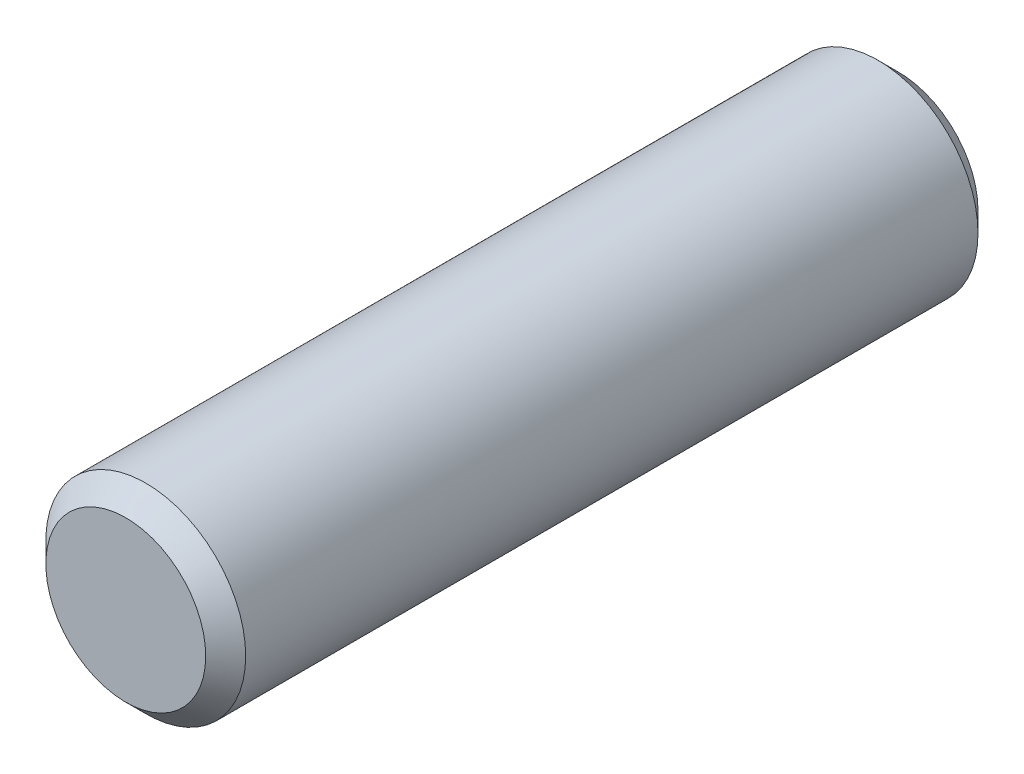
SolidWorks part; units mm, degrees
material "Plain Carbon Steel"
ref_plane "Front" through (0, 0, 0) normal (0, 0, 1) x (1, 0, 0)
ref_plane "Top" through (0, 0, 0) normal (0, 1, 0) x (1, 0, 0)
ref_plane "Right" through (0, 0, 0) normal (1, 0, 0) x (0, 0, -1)
sketch "Sketch1" plane through (0, 0, 0) normal (0, 0, 1) x (1, 0, 0)
  circle A0 centre (0, 0) radius 7.9375
  dimension "Diameter" = 15.875
sketch "Sketch2" plane through (0, 0, 0) normal (1, 0, 0) x (0, 0, -1)
  line L0 (-30.675, 0) -> (30.675, 0) construction
  line L1 (20.125, 7.9375) -> (20.125, -7.9375) construction
  line L2 (8.7312, 0) -> (-8.7312, 0) construction
  line L3 (-20.125, 7.9375) -> (-20.125, -7.9375) construction
  line L4 (-30.675, 7.9375) -> (-30.675, -7.9375) construction
  line L5 (30.675, 7.9375) -> (30.675, -7.9375) construction
  point P3 (20.125, 0)
  point P8 (0, 0)
  point P9 (-20.125, 0)
  point P15 (-30.675, 0)
  point P18 (30.675, 0)
  dimension "D1" = 15.875
  dimension "Length" = 61.35
  dimension "D2" = 50.8
  dimension "D3" = 50.8
sketch "Sketch3" plane through (0, 0, 0) normal (0, 0, 1) x (1, 0, 0)
  circle A0 centre (0, 0) radius 7.9375
  dimension "D1" = 15.875
extrude "Boss-Extrude1" add sketch "Sketch3" along normal mid plane 61.35
chamfer "Chamfer1" distance 1.5875 angle 45 2 edges at (7.9375, 0, -30.675) (7.9375, 0, 30.675)
equation "\"D1@Sketch3\" = \"Diameter@Sketch1\""
equation "\"D1@Boss-Extrude1\" = \"Length@Sketch2\""
equation "\"D1@Chamfer1\" = \"Diameter@Sketch1\" * .1"
equation "\"D1@Sketch2\" = \"Diameter@Sketch1\""
equation "\"Length@Sketch2\"= \"Strut Length@Rocker Bogie Assy.Assembly\" + \"Plate Thickness@Rocker Bogie Assy.Assembly\" * 2 + 5mm"
